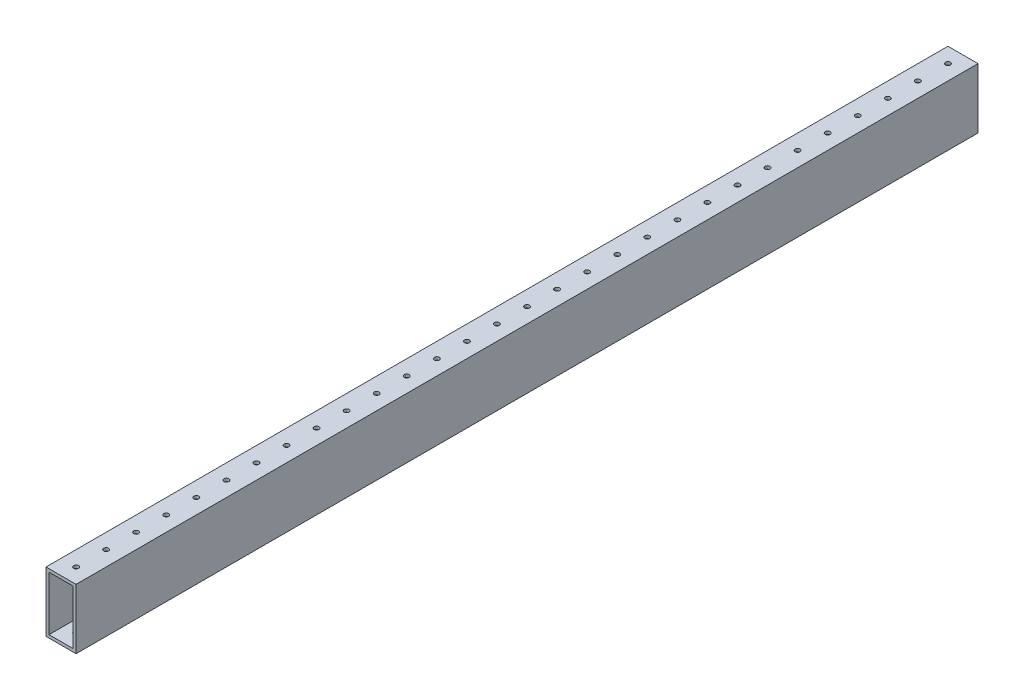
SolidWorks part; units mm, degrees
ref_plane "Front" through (0, 0, 0) normal (0, 0, 1) x (1, 0, 0)
ref_plane "Top" through (0, 0, 0) normal (0, 1, 0) x (1, 0, 0)
ref_plane "Right" through (0, 0, 0) normal (1, 0, 0) x (0, 0, -1)
sketch "Sketch1" plane through (0, 0, 0) normal (0, 0, 1) x (1, 0, 0)
  line L5 (-12.7, -25.4) -> (12.7, -25.4)
  line L6 (-12.7, -25.4) -> (-12.7, 25.4)
  line L7 (-12.7, 25.4) -> (12.7, 25.4)
  line L8 (12.7, -25.4) -> (12.7, 25.4)
  line L9 (-12.7, -25.4) -> (12.7, 25.4) construction
  line L10 (-12.7, 25.4) -> (12.7, -25.4) construction
  point P0 (0, 0)
  dimension "D1" = 50.8
  dimension "D2" = 25.4
extrude "Extrude-Thin1" add sketch "Sketch1" along normal mid plane 762 thin thin type one direction reverse wall 2.54
sketch "Sketch2" plane through (0, 25.4, 0) normal (0, 1, 0) x (1, 0, 0)
  line L0 (0, -381) -> (0, -368.3) construction
  line L1 (12.7, -381) -> (-12.7, -381) construction
  circle A0 centre (0, -368.3) radius 2.0701
  dimension "D1" = 4.1402
  dimension "D2" = 12.7
extrude "Cut-Extrude1" cut sketch "Sketch2" against normal through all
pattern_linear "LPattern1" count 31 spacing 25.4 along (0, 0, -1) of "Cut-Extrude1"
equation "\"lenght\"= 32 - 2"
equation "\"D1@Extrude-Thin1\"=\"lenght\""
equation "\"D1@LPattern1\"=\"lenght\"+1"
